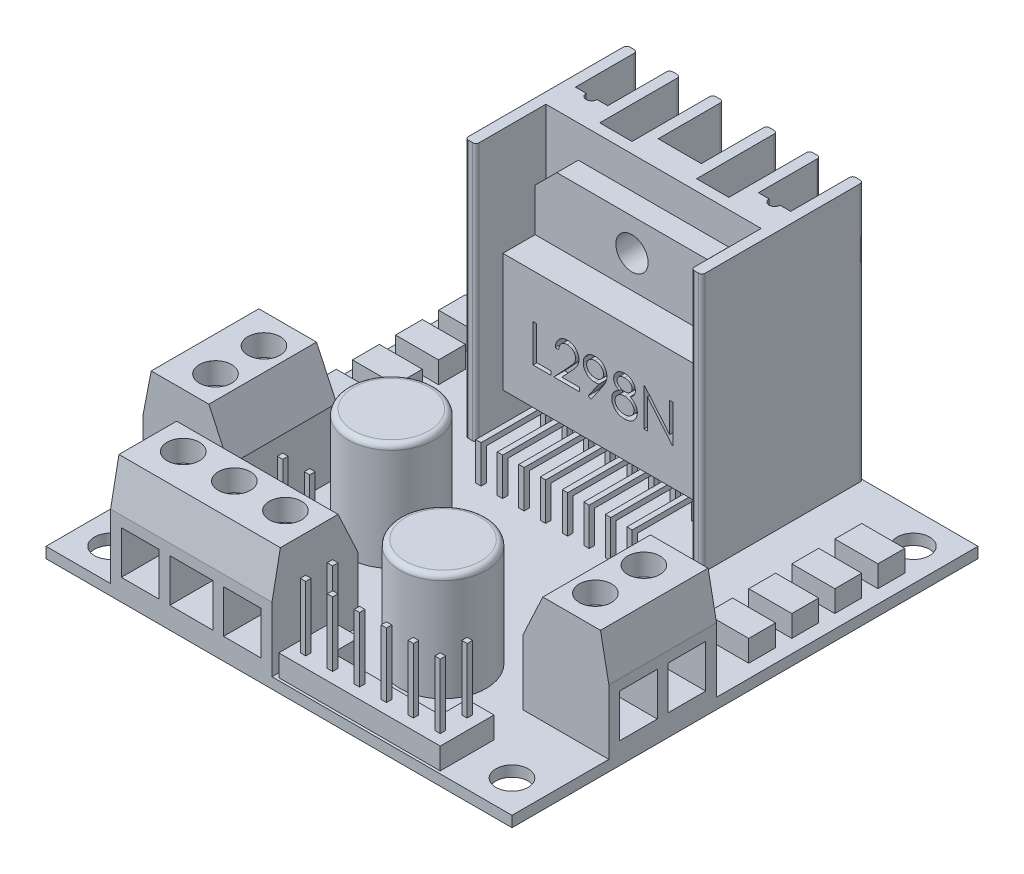
SolidWorks part; units mm, degrees
ref_plane "Alzado" through (0, 0, 0) normal (0, 0, 1) x (1, 0, 0)
ref_plane "Planta" through (0, 0, 0) normal (0, 1, 0) x (1, 0, 0)
ref_plane "Vista lateral" through (0, 0, 0) normal (1, 0, 0) x (0, 0, -1)
sketch "Croquis1" plane through (0, 0, 0) normal (0, 1, 0) x (1, 0, 0)
  line L0 (0, 0) -> (0, -43.3)
  line L1 (0, -43.3) -> (-43.3, -43.3)
  line L2 (-43.3, -43.3) -> (-43.3, 0)
  line L3 (-43.3, 0) -> (0, 0)
  line L4 (-40.3, -40.3) -> (-40.3, -3)
  line L5 (-40.3, -3) -> (-3, -3)
  line L6 (-3, -3) -> (-3, -40.3)
  line L7 (-3, -40.3) -> (-40.3, -40.3)
  circle A0 centre (-40.3, -3) radius 1.5
  circle A1 centre (-3, -3) radius 1.5
  circle A2 centre (-40.3, -40.3) radius 1.5
  circle A3 centre (-3, -40.3) radius 1.5
  dimension "D1" = 3
extrude "Saliente-Extruir1" add sketch "Croquis1" along normal blind 1 contours L3 L2 L1 L0 A3 L7 A2 L4 A0 L5 A1 L6 | A3 L6 A1 L5 A0 L4 A2 L7
sketch "Croquis2" plane through (0, 1, 0) normal (0, 1, 0) x (-1, 0, 0)
  line L0 (10.65, 0) -> (10.65, 15)
  line L1 (43.3, 0) -> (0, 0) construction
  line L3 (32.65, 0) -> (32.65, 15)
  line L4 (21.65, 0) -> (21.65, 15)
  line L5 (32.65, 15) -> (10.65, 15)
  line L6 (28.65, 0) -> (28.65, 15)
  line L7 (14.65, 0) -> (14.65, 15)
  line L8 (18.65, 0) -> (18.65, 15)
  line L9 (24.65, 0) -> (24.65, 15)
  line L10 (32.65, 7.5) -> (10.65, 7.5)
  line L11 (31.65, 0) -> (31.65, 15)
  line L12 (27.65, 0) -> (27.65, 15)
  line L13 (23.65, 0) -> (23.65, 15)
  line L14 (11.65, 0) -> (11.65, 15)
  line L15 (15.65, 0) -> (15.65, 15)
  line L16 (19.65, 0) -> (19.65, 15)
  line L17 (31.65, 5.7532) -> (28.65, 5.7532)
  line L18 (23.65, 6.0647) -> (19.65, 6.0647)
  line L19 (11.65, 5.7532) -> (14.65, 5.7532)
  line L20 (32.65, 8.5) -> (10.65, 8.5)
  circle A0 centre (30.15, 5.7532) radius 0.5042
  circle A1 centre (13.15, 5.7532) radius 0.5042
  line M5 (0, 0) -> (43.3, 0)
  dimension "D1" = 11
  dimension "D2" = 11
  dimension "D3" = 4
  dimension "D4" = 4
  dimension "D5" = 4
  dimension "D6" = 4
  dimension "D7" = 1
  dimension "D8" = 1
  dimension "D9" = 1
  dimension "D10" = 1
  dimension "D11" = 1
  dimension "D12" = 1
  dimension "D13" = 1
extrude "Saliente-Extruir2" add sketch "Croquis2" along normal blind 24 contours L11 L3 L10 M5 | L3 L20 L11 L10 | L20 L3 L5 L11 | L11 L20 L6 L10 | L6 L20 L12 L10 | A0 L17 L11 L10 L6 | L18 L13 L10 L4 | L18 L4 L10 L16 | L13 L9 L10 M5 | L12 L6 L10 M5 | L12 L20 L9 L10 | L9 L20 L13 L10 | L13 L20 L4 L10 | L4 L20 L16 L10 | L16 L20 L8 L10 | L16 L10 L8 M5 | L8 L20 L15 L10 | L15 L20 L7 L10 | L7 L20 L14 L10 | L20 L14 L5 L0 | L14 L20 L0 L10 | L14 L10 L0 M5 | L19 A1 L7 L10 L14 | L15 L10 L7 M5
sketch "Croquis3" plane through (0, 1, 0) normal (0, 1, 0) x (-1, 0, 0)
  line L0 (43.3, 43.3) -> (0, 43.3)
  line L1 (43.3, 34.3) -> (0, 34.3)
  line L2 (43.3, 24.3) -> (0, 24.3)
  line L3 (0, 34.3) -> (0, 24.3)
  line L4 (43.3, 34.3) -> (43.3, 24.3)
  line L5 (35.3, 34.3) -> (35.3, 24.3)
  line L6 (8, 34.3) -> (8, 24.3)
  line M9 (43.3, 0) -> (43.3, 43.3)
  line M11 (0, 43.3) -> (0, 0)
  dimension "D1" = 9
  dimension "D2" = 10
  dimension "D3" = 8
  dimension "D4" = 8
extrude "Saliente-Extruir3" add sketch "Croquis3" along normal blind 10 contours L1 L5 L2 M9 | L6 L1 L2 M11
chamfer "Chaflán1" distance 4 angle 25 1 edges at (-35.3, 11, 29.3)
chamfer "Chaflán2" distance 4 angle 25 1 edges at (-8, 11, 29.3)
chamfer "Chaflán3" distance 4 angle 11 1 edges at (0, 11, 29.3)
chamfer "Chaflán4" distance 4 angle 11 1 edges at (-43.3, 11, 29.3)
sketch "Croquis4" plane through (0, 1, 0) normal (0, 1, 0) x (-1, 0, 0)
  line L0 (35.3, 34.3) -> (37.3, 34.3)
  line L1 (43.3, 34.3) -> (35.3, 34.3) construction
  line L2 (37.3, 34.3) -> (37.3, 43.3)
  line L3 (0, 43.3) -> (43.3, 43.3) construction
  line L4 (37.3, 43.3) -> (22.3, 43.3)
  line L5 (37.3, 35.3) -> (22.3, 35.3)
  line L6 (22.3, 35.3) -> (22.3, 43.3)
  line M24 (43.3, 43.3) -> (0, 43.3)
  dimension "D1" = 8
extrude "Saliente-Extruir4" add sketch "Croquis4" along normal blind 10 contours L6 L5 L2 M24
chamfer "Chaflán5" distance 4 angle 11 1 edges at (-29.8, 11, 43.3)
chamfer "Chaflán6" distance 4 angle 25 1 edges at (-29.8, 11, 35.3)
sketch "Croquis5" plane through (0, 1, 0) normal (0, 1, 0) x (-1, 0, 0)
  line L0 (5.2392, 12.0641) -> (1.2392, 12.0641)
  line L2 (5.2392, 9.5641) -> (5.2392, 12.0641)
  line L3 (5.2392, 5.5641) -> (1.2392, 5.5641)
  line L4 (5.2392, 5.5641) -> (5.2392, 8.0641)
  line L5 (5.2392, 8.0641) -> (1.2392, 8.0641)
  line L6 (1.2392, 5.5641) -> (1.2392, 8.0641)
  line L7 (5.2392, 9.5641) -> (1.2392, 9.5641)
  line L8 (1.2392, 9.5641) -> (1.2392, 12.0641)
  line L9 (5.2392, 16.0641) -> (1.2392, 16.0641)
  line L10 (5.2392, 13.5641) -> (5.2392, 16.0641)
  line L11 (5.2392, 13.5641) -> (1.2392, 13.5641)
  line L12 (1.2392, 13.5641) -> (1.2392, 16.0641)
  line L13 (5.2392, 20.0641) -> (1.2392, 20.0641)
  line L14 (5.2392, 17.5641) -> (5.2392, 20.0641)
  line L15 (5.2392, 17.5641) -> (1.2392, 17.5641)
  line L16 (1.2392, 17.5641) -> (1.2392, 20.0641)
  line L17 (21.65, 8.5) -> (21.65, 17.5641)
  line L18 (31.65, 8.5) -> (11.65, 8.5) construction
  line L19 (42.0608, 17.5641) -> (42.0608, 20.0641)
  line L20 (38.0608, 17.5641) -> (42.0608, 17.5641)
  line L21 (38.0608, 17.5641) -> (38.0608, 20.0641)
  line L22 (38.0608, 20.0641) -> (42.0608, 20.0641)
  line L23 (42.0608, 13.5641) -> (42.0608, 16.0641)
  line L24 (38.0608, 13.5641) -> (42.0608, 13.5641)
  line L25 (38.0608, 13.5641) -> (38.0608, 16.0641)
  line L26 (38.0608, 16.0641) -> (42.0608, 16.0641)
  line L27 (42.0608, 9.5641) -> (42.0608, 12.0641)
  line L28 (38.0608, 9.5641) -> (42.0608, 9.5641)
  line L29 (42.0608, 5.5641) -> (42.0608, 8.0641)
  line L30 (38.0608, 8.0641) -> (42.0608, 8.0641)
  line L31 (38.0608, 5.5641) -> (38.0608, 8.0641)
  line L32 (38.0608, 5.5641) -> (42.0608, 5.5641)
  line L33 (38.0608, 9.5641) -> (38.0608, 12.0641)
  line L34 (38.0608, 12.0641) -> (42.0608, 12.0641)
  dimension "D1" = 4
extrude "Saliente-Extruir5" add sketch "Croquis5" along normal blind 2 contours L34 L33 L28 L27 | L31 L32 L29 L30 | L26 L25 L24 L23 | L22 L21 L20 L19 | L6 L3 L4 L5 | L8 L7 L2 L0 | L12 L11 L10 L9 | L16 L15 L14 L13
sketch "Croquis6" plane through (0, 1, 0) normal (0, 1, 0) x (-1, 0, 0)
  line L0 (35.3, 26.21) -> (28.3, 26.21)
  line L1 (35.3, 34.3) -> (35.3, 24.3) construction
  line L2 (8, 34.3) -> (15.4066, 34.3)
  circle A0 centre (28.3, 26.21) radius 4
  circle A1 centre (15.4066, 34.3) radius 4
extrude "Saliente-Extruir6" add sketch "Croquis6" along normal blind 10
fillet "Redondeo1" radius 0.5 2 edges at (-28.3, 11, 30.21) (-15.4066, 11, 38.3)
sketch "Croquis7" plane through (0, 1, 0) normal (0, 1, 0) x (-1, 0, 0)
  line L0 (16.9077, 40.5596) -> (16.9077, 43.0596)
  line L1 (21.9077, 40.5596) -> (19.4077, 40.5596)
  line L2 (21.9077, 40.5596) -> (21.9077, 43.0596)
  line L3 (21.9077, 43.0596) -> (19.4077, 43.0596)
  line L4 (19.4077, 40.5596) -> (19.4077, 43.0596)
  line L5 (19.4077, 40.5596) -> (16.9077, 40.5596)
  line L6 (19.4077, 43.0596) -> (16.9077, 43.0596)
  line L7 (14.4077, 40.5596) -> (14.4077, 43.0596)
  line L8 (16.9077, 40.5596) -> (14.4077, 40.5596)
  line L9 (16.9077, 43.0596) -> (14.4077, 43.0596)
  line L10 (11.9077, 40.5596) -> (11.9077, 43.0596)
  line L11 (14.4077, 40.5596) -> (11.9077, 40.5596)
  line L12 (14.4077, 43.0596) -> (11.9077, 43.0596)
  line L13 (9.4077, 40.5596) -> (9.4077, 43.0596)
  line L14 (11.9077, 40.5596) -> (9.4077, 40.5596)
  line L15 (11.9077, 43.0596) -> (9.4077, 43.0596)
  line L16 (6.9077, 40.5596) -> (6.9077, 43.0596)
  line L17 (9.4077, 40.5596) -> (6.9077, 40.5596)
  line L18 (9.4077, 43.0596) -> (6.9077, 43.0596)
  line L19 (19.4077, 38.0596) -> (19.4077, 40.5596)
  line L20 (21.9077, 38.0596) -> (19.4077, 38.0596)
  line L21 (21.9077, 40.5596) -> (19.4077, 40.5596)
  line L22 (16.9077, 38.0596) -> (16.9077, 40.5596)
  line L23 (19.4077, 38.0596) -> (16.9077, 38.0596)
  line L24 (19.4077, 40.5596) -> (16.9077, 40.5596)
  line L25 (14.4077, 38.0596) -> (14.4077, 40.5596)
  line L26 (16.9077, 38.0596) -> (14.4077, 38.0596)
  line L27 (16.9077, 40.5596) -> (14.4077, 40.5596)
  line L28 (11.9077, 38.0596) -> (11.9077, 40.5596)
  line L29 (14.4077, 38.0596) -> (11.9077, 38.0596)
  line L30 (14.4077, 40.5596) -> (11.9077, 40.5596)
  line L31 (9.4077, 38.0596) -> (9.4077, 40.5596)
  line L32 (11.9077, 38.0596) -> (9.4077, 38.0596)
  line L33 (11.9077, 40.5596) -> (9.4077, 40.5596)
  line L34 (6.9077, 38.0596) -> (6.9077, 40.5596)
  line L35 (9.4077, 38.0596) -> (6.9077, 38.0596)
  line L36 (9.4077, 40.5596) -> (6.9077, 40.5596)
  line L37 (21.9077, 38.0596) -> (21.9077, 40.5596)
  line L38 (21.9077, 40.5596) -> (21.8661, 40.5089)
  dimension "D1" = 6
  dimension "D2" = 2
extrude "Saliente-Extruir7" add sketch "Croquis7" along normal blind 2
sketch "Croquis8" plane through (0, 1, 0) normal (0, 1, 0) x (-1, 0, 0)
  line L0 (30.3, 34.3) -> (30.3, 31.8)
  line L1 (35.3, 34.3) -> (32.8, 34.3)
  line L2 (35.3, 34.3) -> (35.3, 31.8)
  line L3 (35.3, 31.8) -> (32.8, 31.8)
  line L4 (32.8, 34.3) -> (32.8, 31.8)
  line L5 (32.8, 34.3) -> (30.3, 34.3)
  line L6 (32.8, 31.8) -> (30.3, 31.8)
  line L7 (27.8, 34.3) -> (27.8, 31.8)
  line L8 (30.3, 34.3) -> (27.8, 34.3)
  line L9 (30.3, 31.8) -> (27.8, 31.8)
  dimension "D1" = 3
extrude "Saliente-Extruir8" add sketch "Croquis8" along normal blind 2 contours L9 L0 L8 L7 | L6 L4 L5 L0
sketch "Croquis9" plane through (0, 3, 0) normal (0, 1, 0) x (-1, 0, 0)
  line L0 (21.9077, 43.0596) -> (6.9077, 43.0596)
  line L1 (21.9077, 41.8096) -> (6.9077, 41.8096)
  line L2 (21.9077, 43.0596) -> (21.9077, 38.0596)
  line L3 (21.9077, 38.0596) -> (19.4077, 38.0596) construction
  line L4 (21.9077, 38.0596) -> (21.9077, 43.0596) construction
  line L5 (20.6577, 43.0596) -> (20.6577, 38.0596)
  line L7 (17.9077, 42.0596) -> (17.9077, 41.5596)
  line L8 (8.1577, 38.0596) -> (8.1577, 43.0596)
  line L9 (8.1577, 38.0596) -> (8.1577, 43.0596)
  line L10 (20.4077, 42.0596) -> (20.9077, 42.0596)
  line L11 (20.4077, 42.0596) -> (20.4077, 41.5596)
  line L12 (20.4077, 41.5596) -> (20.9077, 41.5596)
  line L13 (20.9077, 42.0596) -> (20.9077, 41.5596)
  line L14 (20.4077, 42.0596) -> (20.9077, 41.5596) construction
  line L15 (20.4077, 41.5596) -> (20.9077, 42.0596) construction
  line L16 (17.9077, 41.5596) -> (18.4077, 41.5596)
  line L17 (18.4077, 42.0596) -> (18.4077, 41.5596)
  line L18 (17.9077, 42.0596) -> (18.4077, 42.0596)
  line L19 (15.4077, 42.0596) -> (15.4077, 41.5596)
  line L20 (15.4077, 41.5596) -> (15.9077, 41.5596)
  line L21 (15.9077, 42.0596) -> (15.9077, 41.5596)
  line L22 (15.4077, 42.0596) -> (15.9077, 42.0596)
  line L23 (12.9077, 42.0596) -> (12.9077, 41.5596)
  line L24 (12.9077, 41.5596) -> (13.4077, 41.5596)
  line L25 (13.4077, 42.0596) -> (13.4077, 41.5596)
  line L26 (12.9077, 42.0596) -> (13.4077, 42.0596)
  line L27 (10.4077, 42.0596) -> (10.4077, 41.5596)
  line L28 (10.4077, 41.5596) -> (10.9077, 41.5596)
  line L29 (10.9077, 42.0596) -> (10.9077, 41.5596)
  line L30 (10.4077, 42.0596) -> (10.9077, 42.0596)
  line L31 (7.9077, 42.0596) -> (7.9077, 41.5596)
  line L32 (7.9077, 41.5596) -> (8.4077, 41.5596)
  line L33 (8.4077, 42.0596) -> (8.4077, 41.5596)
  line L34 (7.9077, 42.0596) -> (8.4077, 42.0596)
  line L35 (20.4077, 39.5596) -> (20.4077, 39.0596)
  line L36 (20.4077, 39.0596) -> (20.9077, 39.0596)
  line L37 (20.9077, 39.5596) -> (20.9077, 39.0596)
  line L38 (20.4077, 39.5596) -> (20.9077, 39.5596)
  line L39 (17.9077, 39.5596) -> (17.9077, 39.0596)
  line L40 (17.9077, 39.0596) -> (18.4077, 39.0596)
  line L41 (18.4077, 39.5596) -> (18.4077, 39.0596)
  line L42 (17.9077, 39.5596) -> (18.4077, 39.5596)
  line L43 (15.4077, 39.5596) -> (15.4077, 39.0596)
  line L44 (15.4077, 39.0596) -> (15.9077, 39.0596)
  line L45 (15.9077, 39.5596) -> (15.9077, 39.0596)
  line L46 (15.4077, 39.5596) -> (15.9077, 39.5596)
  line L47 (12.9077, 39.5596) -> (12.9077, 39.0596)
  line L48 (12.9077, 39.0596) -> (13.4077, 39.0596)
  line L49 (13.4077, 39.5596) -> (13.4077, 39.0596)
  line L50 (12.9077, 39.5596) -> (13.4077, 39.5596)
  line L51 (10.4077, 39.5596) -> (10.4077, 39.0596)
  line L52 (10.4077, 39.0596) -> (10.9077, 39.0596)
  line L53 (10.9077, 39.5596) -> (10.9077, 39.0596)
  line L54 (10.4077, 39.5596) -> (10.9077, 39.5596)
  line L55 (7.9077, 39.5596) -> (7.9077, 39.0596)
  line L56 (7.9077, 39.0596) -> (8.4077, 39.0596)
  line L57 (8.4077, 39.5596) -> (8.4077, 39.0596)
  line L58 (7.9077, 39.5596) -> (8.4077, 39.5596)
  point P13 (20.6577, 41.8096)
  dimension "D4" = 6
  dimension "D1" = 1.25
  dimension "D2" = 1.25
  dimension "D3" = 1.25
  dimension "D5" = 2
extrude "Saliente-Extruir9" add sketch "Croquis9" along normal blind 6 contours L10 L11 L1 L5 | L11 L12 L5 L1 | L13 L10 L5 L1 | L13 L1 L5 L12 | L38 L35 L36 L5 | L38 L5 L36 L37 | L17 L1 L7 L16 | L18 L7 L1 L17 | L21 L1 L19 L20 | L22 L19 L1 L21 | L26 L23 L1 L25 | L25 L1 L23 L24 | L30 L27 L1 L29 | L29 L1 L27 L28 | L34 L31 L1 L9 | L31 L32 L9 L1 | L33 L1 L9 L32 | L34 L9 L1 L33 | L58 L55 L56 L9 | L58 L9 L56 L57
sketch "Croquis10" plane through (0, 3, 0) normal (0, 1, 0) x (1, 0, 0)
  line L0 (-32.8, -34.3) -> (-27.8, -34.3)
  line L1 (-27.8, -34.3) -> (-27.8, -31.8)
  line L2 (-32.8, -33.05) -> (-27.8, -33.05)
  line L3 (-29.05, -34.3) -> (-29.05, -31.8)
  line L5 (-28.8, -33.3) -> (-28.8, -32.8)
  line L6 (-31.55, -34.3) -> (-31.55, -31.8)
  line L7 (-31.55, -34.3) -> (-31.55, -31.8)
  line L8 (-31.8, -33.3) -> (-31.3, -33.3)
  line L9 (-31.8, -33.3) -> (-31.8, -32.8)
  line L10 (-31.8, -32.8) -> (-31.3, -32.8)
  line L11 (-31.3, -33.3) -> (-31.3, -32.8)
  line L12 (-31.8, -33.3) -> (-31.3, -32.8) construction
  line L13 (-31.8, -32.8) -> (-31.3, -33.3) construction
  line L14 (-29.3, -33.3) -> (-28.8, -33.3)
  line L15 (-29.3, -32.8) -> (-28.8, -32.8)
  line L16 (-29.3, -33.3) -> (-29.3, -32.8)
  point P11 (-31.55, -33.05)
  dimension "D4" = 2
  dimension "D1" = 1.25
  dimension "D2" = 1.25
  dimension "D3" = 1.25
extrude "Saliente-Extruir10" add sketch "Croquis10" along normal blind 6 contours L11 L10 L9 L8 | L15 L5 L14 L16
sketch "Croquis11" plane through (0, 0, 8.5) normal (0, 0, 1) x (1, 0, 0)
  line L0 (-21.65, 25) -> (-21.65, 1)
  line L1 (-31.65, 25) -> (-11.65, 25) construction
  line L2 (-31.65, 1) -> (-11.65, 1) construction
  line L3 (-30.65, 25) -> (-30.65, 1)
  line L4 (-12.65, 25) -> (-12.65, 1)
  line L5 (-31.65, 22) -> (-11.65, 22)
  line L6 (-31.65, 22) -> (-11.65, 22)
  line L7 (-31.65, 15) -> (-11.65, 15)
  line L8 (-31.65, 5) -> (-11.65, 5)
  line L9 (-30.65, 19.9875) -> (-28.6375, 22)
  line L10 (-12.65, 19.9875) -> (-14.6625, 22)
  dimension "D1" = 3
  dimension "D2" = 9
  dimension "D3" = 9
  dimension "D4" = 7
  dimension "D5" = 10
extrude "Saliente-Extruir11" add sketch "Croquis11" along normal blind 5 contours L9 L3 L7 L0 L6 | L4 L10 L6 L0 L7 | L3 L8 L0 L7 | L0 L8 L4 L7
sketch "Croquis12" plane through (0, 0, 13.5) normal (0, 0, 1) x (1, 0, 0)
  line L0 (-30.65, 22) -> (-12.65, 22)
  line L1 (-30.65, 16) -> (-12.65, 16)
  line L2 (-30.65, 22) -> (-30.65, 16)
  line L3 (-12.65, 22) -> (-12.65, 16)
  line L4 (-12.65, 16) -> (-12.6059, 15.8404)
  line M2 (-12.65, 5) -> (-12.65, 19.9875)
  line M3 (-12.65, 19.9875) -> (-14.6625, 22)
  line M4 (-14.6625, 22) -> (-28.6375, 22)
  line M5 (-28.6375, 22) -> (-30.65, 19.9875)
  line M6 (-30.65, 19.9875) -> (-30.65, 5)
  dimension "D1" = 6
extrude "Cortar-Extruir1" cut sketch "Croquis12" against normal blind 3 contours L1 M6 M2 M3 M4 M5
sketch "Croquis13" plane through (0, 5, 0) normal (0, -1, 0) x (1, 0, 0)
  line L0 (-30.65, 11) -> (-12.65, 11)
  line L1 (-30.65, 13.5) -> (-30.65, 8.5) construction
  line L2 (-12.65, 13.5) -> (-12.65, 8.5) construction
  line L3 (-28.4231, 11.25) -> (-27.9231, 11.25)
  line L4 (-29.4231, 11.25) -> (-28.9231, 11.25)
  line L5 (-29.4231, 11.25) -> (-29.4231, 10.75)
  line L6 (-29.4231, 10.75) -> (-28.9231, 10.75)
  line L7 (-28.9231, 11.25) -> (-28.9231, 10.75)
  line L8 (-29.4231, 11.25) -> (-28.9231, 10.75) construction
  line L9 (-29.4231, 10.75) -> (-28.9231, 11.25) construction
  line L10 (-27.9231, 11.25) -> (-27.9231, 10.75)
  line L11 (-28.4231, 10.75) -> (-27.9231, 10.75)
  line L12 (-28.4231, 11.25) -> (-28.4231, 10.75)
  line L13 (-27.4231, 11.25) -> (-26.9231, 11.25)
  line L14 (-26.9231, 11.25) -> (-26.9231, 10.75)
  line L15 (-27.4231, 10.75) -> (-26.9231, 10.75)
  line L16 (-27.4231, 11.25) -> (-27.4231, 10.75)
  line L17 (-26.4231, 11.25) -> (-25.9231, 11.25)
  line L18 (-25.9231, 11.25) -> (-25.9231, 10.75)
  line L19 (-26.4231, 10.75) -> (-25.9231, 10.75)
  line L20 (-26.4231, 11.25) -> (-26.4231, 10.75)
  line L21 (-25.4231, 11.25) -> (-24.9231, 11.25)
  line L22 (-24.9231, 11.25) -> (-24.9231, 10.75)
  line L23 (-25.4231, 10.75) -> (-24.9231, 10.75)
  line L24 (-25.4231, 11.25) -> (-25.4231, 10.75)
  line L25 (-24.4231, 11.25) -> (-23.9231, 11.25)
  line L26 (-23.9231, 11.25) -> (-23.9231, 10.75)
  line L27 (-24.4231, 10.75) -> (-23.9231, 10.75)
  line L28 (-24.4231, 11.25) -> (-24.4231, 10.75)
  line L29 (-23.4231, 11.25) -> (-22.9231, 11.25)
  line L30 (-22.9231, 11.25) -> (-22.9231, 10.75)
  line L31 (-23.4231, 10.75) -> (-22.9231, 10.75)
  line L32 (-23.4231, 11.25) -> (-23.4231, 10.75)
  line L33 (-22.4231, 11.25) -> (-21.9231, 11.25)
  line L34 (-21.9231, 11.25) -> (-21.9231, 10.75)
  line L35 (-22.4231, 10.75) -> (-21.9231, 10.75)
  line L36 (-22.4231, 11.25) -> (-22.4231, 10.75)
  line L37 (-21.65, 11) -> (-21.65, 9.6943)
  line L38 (-13.8769, 10.75) -> (-14.3769, 11.25) construction
  line L39 (-13.8769, 11.25) -> (-14.3769, 10.75) construction
  line L40 (-20.8769, 11.25) -> (-20.8769, 10.75)
  line L41 (-20.8769, 10.75) -> (-21.3769, 10.75)
  line L42 (-21.3769, 11.25) -> (-21.3769, 10.75)
  line L43 (-20.8769, 11.25) -> (-21.3769, 11.25)
  line L44 (-19.8769, 11.25) -> (-19.8769, 10.75)
  line L45 (-19.8769, 10.75) -> (-20.3769, 10.75)
  line L46 (-20.3769, 11.25) -> (-20.3769, 10.75)
  line L47 (-19.8769, 11.25) -> (-20.3769, 11.25)
  line L48 (-18.8769, 11.25) -> (-18.8769, 10.75)
  line L49 (-18.8769, 10.75) -> (-19.3769, 10.75)
  line L50 (-19.3769, 11.25) -> (-19.3769, 10.75)
  line L51 (-18.8769, 11.25) -> (-19.3769, 11.25)
  line L52 (-17.8769, 11.25) -> (-17.8769, 10.75)
  line L53 (-17.8769, 10.75) -> (-18.3769, 10.75)
  line L54 (-18.3769, 11.25) -> (-18.3769, 10.75)
  line L55 (-17.8769, 11.25) -> (-18.3769, 11.25)
  line L56 (-16.8769, 11.25) -> (-16.8769, 10.75)
  line L57 (-16.8769, 10.75) -> (-17.3769, 10.75)
  line L58 (-17.3769, 11.25) -> (-17.3769, 10.75)
  line L59 (-16.8769, 11.25) -> (-17.3769, 11.25)
  line L60 (-15.8769, 11.25) -> (-15.8769, 10.75)
  line L61 (-15.8769, 10.75) -> (-16.3769, 10.75)
  line L62 (-16.3769, 11.25) -> (-16.3769, 10.75)
  line L63 (-15.8769, 11.25) -> (-16.3769, 11.25)
  line L64 (-14.8769, 11.25) -> (-14.8769, 10.75)
  line L65 (-14.8769, 10.75) -> (-15.3769, 10.75)
  line L66 (-15.3769, 11.25) -> (-15.3769, 10.75)
  line L67 (-14.3769, 11.25) -> (-14.3769, 10.75)
  line L68 (-13.8769, 10.75) -> (-14.3769, 10.75)
  line L69 (-13.8769, 11.25) -> (-13.8769, 10.75)
  line L70 (-13.8769, 11.25) -> (-14.3769, 11.25)
  line L71 (-14.8769, 11.25) -> (-15.3769, 11.25)
  point P6 (-29.1731, 11)
  point P73 (-14.1269, 11)
  dimension "D1" = 8
extrude "Saliente-Extruir12" add sketch "Croquis13" along normal blind 1 contours L68 L67 L70 L69 | L65 L66 L71 L64 | L63 L62 L61 L60 | L59 L58 L57 L56 | L55 L54 L53 L52 | L51 L50 L49 L48 | L47 L46 L45 L44 | L43 L42 L41 L40 | L33 L34 L35 L36 | L29 L30 L31 L32 | L25 L26 L27 L28 | L21 L22 L23 L24 | L17 L18 L19 L20 | L13 L14 L15 L16 | L3 L10 L11 L12 | L4 L7 L6 L5
sketch "Croquis14" plane through (0, 0, 11.25) normal (0, 0, 1) x (1, 0, 0)
  line L0 (-14.3769, 4) -> (-14.3769, 5) construction
  line L1 (-13.8769, 4) -> (-14.3769, 4)
  line L2 (-13.8769, 4) -> (-13.8769, 4.5)
  line L3 (-13.8769, 4.5) -> (-14.3769, 4.5)
  line L4 (-14.3769, 4) -> (-14.3769, 4.5)
  line L5 (-15.8769, 4) -> (-15.8769, 4.5)
  line L6 (-15.8769, 4.5) -> (-16.3769, 4.5)
  line L7 (-16.3769, 4) -> (-16.3769, 4.5)
  line L8 (-15.8769, 4) -> (-16.3769, 4)
  line L9 (-17.8769, 4) -> (-17.8769, 4.5)
  line L10 (-17.8769, 4.5) -> (-18.3769, 4.5)
  line L11 (-18.3769, 4) -> (-18.3769, 4.5)
  line L12 (-17.8769, 4) -> (-18.3769, 4)
  line L13 (-19.8769, 4) -> (-19.8769, 4.5)
  line L14 (-19.8769, 4.5) -> (-20.3769, 4.5)
  line L15 (-20.3769, 4) -> (-20.3769, 4.5)
  line L16 (-19.8769, 4) -> (-20.3769, 4)
  line L17 (-22.4231, 4) -> (-22.4231, 5) construction
  line L18 (-21.9231, 4) -> (-22.4231, 4)
  line L19 (-21.9231, 4) -> (-21.9231, 4.5)
  line L20 (-21.9231, 4.5) -> (-22.4231, 4.5)
  line L21 (-22.4231, 4) -> (-22.4231, 4.5)
  line L22 (-23.9231, 4) -> (-23.9231, 4.5)
  line L23 (-23.9231, 4) -> (-24.4231, 4)
  line L24 (-24.4231, 4) -> (-24.4231, 4.5)
  line L25 (-23.9231, 4.5) -> (-24.4231, 4.5)
  line L26 (-25.9231, 4) -> (-25.9231, 4.5)
  line L27 (-25.9231, 4) -> (-26.4231, 4)
  line L28 (-26.4231, 4) -> (-26.4231, 4.5)
  line L29 (-25.9231, 4.5) -> (-26.4231, 4.5)
  line L30 (-27.9231, 4) -> (-27.9231, 4.5)
  line L31 (-27.9231, 4) -> (-28.4231, 4)
  line L32 (-28.4231, 4) -> (-28.4231, 4.5)
  line L33 (-27.9231, 4.5) -> (-28.4231, 4.5)
  dimension "D1" = 4
  dimension "D2" = 4
extrude "Saliente-Extruir13" add sketch "Croquis14" along normal blind 7
sketch "Croquis15" plane through (0, 0, 0) normal (0, -1, 0) x (1, 0, 0)
  line L0 (-27.9231, 18.25) -> (-27.9231, 10.75) construction
  line L1 (-28.4231, 18.25) -> (-27.9231, 18.25)
  line L2 (-28.4231, 18.25) -> (-28.4231, 17.75)
  line L3 (-28.4231, 17.75) -> (-27.9231, 17.75)
  line L4 (-27.9231, 18.25) -> (-27.9231, 17.75)
  line L5 (-25.9231, 18.25) -> (-25.9231, 17.75)
  line L6 (-26.4231, 18.25) -> (-25.9231, 18.25)
  line L7 (-26.4231, 18.25) -> (-26.4231, 17.75)
  line L8 (-26.4231, 17.75) -> (-25.9231, 17.75)
  line L9 (-23.9231, 18.25) -> (-23.9231, 17.75)
  line L10 (-24.4231, 18.25) -> (-23.9231, 18.25)
  line L11 (-24.4231, 18.25) -> (-24.4231, 17.75)
  line L12 (-24.4231, 17.75) -> (-23.9231, 17.75)
  line L13 (-21.9231, 18.25) -> (-21.9231, 17.75)
  line L14 (-22.4231, 18.25) -> (-21.9231, 18.25)
  line L15 (-22.4231, 18.25) -> (-22.4231, 17.75)
  line L16 (-22.4231, 17.75) -> (-21.9231, 17.75)
  line L17 (-19.8769, 18.25) -> (-19.8769, 10.75) construction
  line L18 (-20.3769, 18.25) -> (-19.8769, 18.25)
  line L19 (-20.3769, 18.25) -> (-20.3769, 17.75)
  line L20 (-20.3769, 17.75) -> (-19.8769, 17.75)
  line L21 (-19.8769, 18.25) -> (-19.8769, 17.75)
  line L22 (-17.8769, 18.25) -> (-17.8769, 10.75) construction
  line L23 (-18.3769, 18.25) -> (-17.8769, 18.25)
  line L24 (-18.3769, 18.25) -> (-18.3769, 17.75)
  line L25 (-18.3769, 17.75) -> (-17.8769, 17.75)
  line L26 (-17.8769, 18.25) -> (-17.8769, 17.75)
  line L27 (-15.8769, 18.25) -> (-15.8769, 10.75) construction
  line L28 (-16.3769, 18.25) -> (-15.8769, 18.25)
  line L29 (-16.3769, 18.25) -> (-16.3769, 17.75)
  line L30 (-16.3769, 17.75) -> (-15.8769, 17.75)
  line L31 (-15.8769, 18.25) -> (-15.8769, 17.75)
  line L32 (-13.8769, 18.25) -> (-13.8769, 10.75) construction
  line L33 (-14.3769, 18.25) -> (-13.8769, 18.25)
  line L34 (-14.3769, 18.25) -> (-14.3769, 17.75)
  line L35 (-14.3769, 17.75) -> (-13.8769, 17.75)
  line L36 (-13.8769, 18.25) -> (-13.8769, 17.75)
  dimension "D1" = 4
extrude "Saliente-Extruir14" add sketch "Croquis15" against normal blind 4
sketch "Croquis16" plane through (0, 0, 0) normal (0, -1, 0) x (1, 0, 0)
  line L0 (-22.9231, 11.25) -> (-22.9231, 10.75) construction
  line L1 (-29.4231, 11.25) -> (-28.9231, 11.25)
  line L2 (-29.4231, 11.25) -> (-29.4231, 10.75)
  line L3 (-29.4231, 10.75) -> (-28.9231, 10.75)
  line L4 (-28.9231, 11.25) -> (-28.9231, 10.75)
  line L5 (-27.4231, 11.25) -> (-26.9231, 11.25)
  line L6 (-27.4231, 11.25) -> (-27.4231, 10.75)
  line L7 (-27.4231, 10.75) -> (-26.9231, 10.75)
  line L8 (-26.9231, 11.25) -> (-26.9231, 10.75)
  line L9 (-25.4231, 11.25) -> (-24.9231, 11.25)
  line L10 (-25.4231, 11.25) -> (-25.4231, 10.75)
  line L11 (-25.4231, 10.75) -> (-24.9231, 10.75)
  line L12 (-24.9231, 11.25) -> (-24.9231, 10.75)
  line L13 (-23.4231, 11.25) -> (-22.9231, 11.25)
  line L14 (-23.4231, 11.25) -> (-23.4231, 10.75)
  line L15 (-23.4231, 10.75) -> (-22.9231, 10.75)
  line L16 (-22.9231, 11.25) -> (-22.9231, 10.75)
  line L18 (-21.3769, 11.25) -> (-20.8769, 11.25)
  line L19 (-21.3769, 11.25) -> (-21.3769, 10.75)
  line L20 (-21.3769, 10.75) -> (-20.8769, 10.75)
  line L21 (-20.8769, 11.25) -> (-20.8769, 10.75)
  line L22 (-19.3769, 11.25) -> (-18.8769, 11.25)
  line L23 (-19.3769, 11.25) -> (-19.3769, 10.75)
  line L24 (-19.3769, 10.75) -> (-18.8769, 10.75)
  line L25 (-18.8769, 11.25) -> (-18.8769, 10.75)
  line L26 (-17.3769, 11.25) -> (-16.8769, 11.25)
  line L27 (-17.3769, 11.25) -> (-17.3769, 10.75)
  line L28 (-17.3769, 10.75) -> (-16.8769, 10.75)
  line L29 (-16.8769, 11.25) -> (-16.8769, 10.75)
  line L30 (-15.3769, 11.25) -> (-14.8769, 11.25)
  line L31 (-15.3769, 11.25) -> (-15.3769, 10.75)
  line L32 (-15.3769, 10.75) -> (-14.8769, 10.75)
  line L33 (-14.8769, 11.25) -> (-14.8769, 10.75)
extrude "Saliente-Extruir15" add sketch "Croquis16" against normal blind 4
sketch "Croquis17" plane through (0, 0, 13.5) normal (0, 0, 1) x (1, 0, 0)
  text T0 "L298N"
extrude "Cortar-Extruir2" cut sketch "Croquis17" against normal blind 1
sketch "Croquis18" plane through (0, 0, 10.5) normal (0, 0, 1) x (1, 0, 0)
  line L2 (-14.6625, 19) -> (-28.6375, 19)
  line L3 (-14.6625, 19) -> (-28.6375, 19)
  circle A0 centre (-21.65, 19) radius 1.5
  dimension "D1" = 3
extrude "Cortar-Extruir3" cut sketch "Croquis18" against normal through all contours A0
sketch "Croquis19" plane through (0, 0, 0) normal (1, 0, 0) x (0, 0, -1)
  line L2 (-24.3, 6) -> (-34.3, 6)
  line L3 (-24.3, 6) -> (-34.3, 6)
  line L5 (-33.3, 7) -> (-33.3, 1)
  line L6 (-33.3, 7) -> (-33.3, 1)
  line L8 (-25.3, 7) -> (-25.3, 1)
  line L9 (-25.3, 7) -> (-25.3, 1)
  line L10 (-29.3, 6) -> (-29.3, 2)
  line L11 (0, 2) -> (-43.3, 2)
  line L12 (0, 2) -> (-43.3, 2)
  line L13 (-29.8, 6) -> (-29.8, 2)
  line L14 (-28.8, 6) -> (-28.8, 2)
  dimension "D1" = 1
  dimension "D2" = 1
  dimension "D3" = 1
  dimension "D4" = 2
  dimension "D5" = 0.5
  dimension "D6" = 0.5
extrude "Cortar-Extruir4" cut sketch "Croquis19" against normal blind 4 contours L13 L3 L6 L12 | L3 L14 L12 L9
sketch "Croquis20" plane through (0, 0, 43.3) normal (0, 0, 1) x (1, 0, 0)
  line L2 (-22.3, 6) -> (-37.3, 6)
  line L3 (-22.3, 6) -> (-37.3, 6)
  line L5 (-36.3, 7) -> (-36.3, 1)
  line L6 (-36.3, 7) -> (-36.3, 1)
  line L8 (-23.3, 7) -> (-23.3, 1)
  line L9 (-23.3, 7) -> (-23.3, 1)
  line L10 (-26.8, 7) -> (-26.8, 1)
  line L11 (0, 2) -> (-43.3, 2)
  line L12 (0, 2) -> (-43.3, 2)
  line L13 (-32.8, 7) -> (-32.8, 1)
  line L14 (-31.8, 7) -> (-31.8, 1)
  line L15 (-27.8, 7) -> (-27.8, 1)
  dimension "D1" = 1
  dimension "D2" = 1
  dimension "D3" = 1
  dimension "D4" = 2
  dimension "D5" = 3.5
  dimension "D6" = 3.5
  dimension "D7" = 1
  dimension "D8" = 1
extrude "Cortar-Extruir5" cut sketch "Croquis20" against normal blind 4 contours L13 L3 L6 L12 | L15 L3 L14 L12 | L12 L9 L3 L10
sketch "Croquis21" plane through (-43.3, 0, 0) normal (-1, 0, 0) x (0, 0, 1)
  line L0 (25.3, 2) -> (33.3, 2)
  line L2 (34.3, 6) -> (24.3, 6)
  line L3 (34.3, 6) -> (24.3, 6)
  line L5 (25.3, 7) -> (25.3, 1)
  line L6 (25.3, 7) -> (25.3, 1)
  line L8 (33.3, 7) -> (33.3, 1)
  line L9 (33.3, 7) -> (33.3, 1)
  line L17 (29.8, 7) -> (29.8, 1)
  line L18 (28.8, 7) -> (28.8, 1)
  line L25 (33.3, 1) -> (33.3, 6)
  line L26 (33.3, 6) -> (25.3, 6)
  line L27 (25.3, 6) -> (25.3, 1)
  line L28 (25.3, 1) -> (33.3, 1)
  line L29 (33.3, 1) -> (33.3, 6)
  line L30 (33.3, 6) -> (25.3, 6)
  line L31 (25.3, 6) -> (25.3, 1)
  line L32 (25.3, 1) -> (33.3, 1)
  dimension "D7" = 1
  dimension "D1" = 1
  dimension "D2" = 1
  dimension "D3" = 1
  dimension "D4" = 1
  dimension "D5" = 3.5
  dimension "D6" = 3.5
extrude "Cortar-Extruir6" cut sketch "Croquis21" against normal blind 4 contours L18 L3 L6 L0 | L3 L17 L0 L9
sketch "Croquis22" plane through (0, 11, 0) normal (0, 1, 0) x (-1, 0, 0)
  line L0 (3.4561, 24.3) -> (3.4561, 34.3)
  line L1 (6.1348, 24.3) -> (0.7775, 24.3) construction
  line L2 (6.1348, 34.3) -> (0.7775, 34.3) construction
  line L3 (22.3, 39.8439) -> (37.3, 39.8439)
  line L4 (22.3, 37.1652) -> (22.3, 42.5225) construction
  line L5 (37.3, 37.1652) -> (37.3, 42.5225) construction
  line L6 (39.8439, 34.3) -> (39.8439, 24.3)
  line L7 (42.5225, 34.3) -> (37.1652, 34.3) construction
  line L8 (42.5225, 24.3) -> (37.1652, 24.3) construction
  line L9 (39.3, 28.8) -> (39.3, 25.3) construction
  line L10 (39.3, 33.3) -> (39.3, 29.8) construction
  line L11 (32.8, 39.3) -> (36.3, 39.3) construction
  line L12 (27.8, 39.3) -> (31.8, 39.3) construction
  line L13 (23.3, 39.3) -> (26.8, 39.3) construction
  line L14 (4, 29.8) -> (4, 33.3) construction
  line L15 (4, 25.3) -> (4, 28.8) construction
  circle A0 centre (39.3, 27.05) radius 1.5
  circle A1 centre (39.3, 31.55) radius 1.5
  circle A2 centre (34.55, 39.3) radius 1.5
  circle A3 centre (29.8, 39.3) radius 1.5
  circle A4 centre (25.05, 39.3) radius 1.5
  circle A5 centre (4, 31.55) radius 1.5
  circle A6 centre (4, 27.05) radius 1.5
extrude "Cortar-Extruir7" cut sketch "Croquis22" against normal blind 2 contours A0 | A1 | A2 | A3 | A4 | A5 | A6
fillet "Redondeo2" radius 0.3 16 edges at (-31.65, 13, 0) (-32.65, 13, 0) (-27.65, 13, 0) (-28.65, 13, 0) (-23.65, 13, 0) (-24.65, 13, 0) (-18.65, 13, 0) (-19.65, 13, 0) (-14.65, 13, 0) (-15.65, 13, 0) (-10.65, 13, 0) (-11.65, 13, 0) (-32.65, 13, 15) (-31.65, 13, 15) (-11.65, 13, 15) (-10.65, 13, 15)
